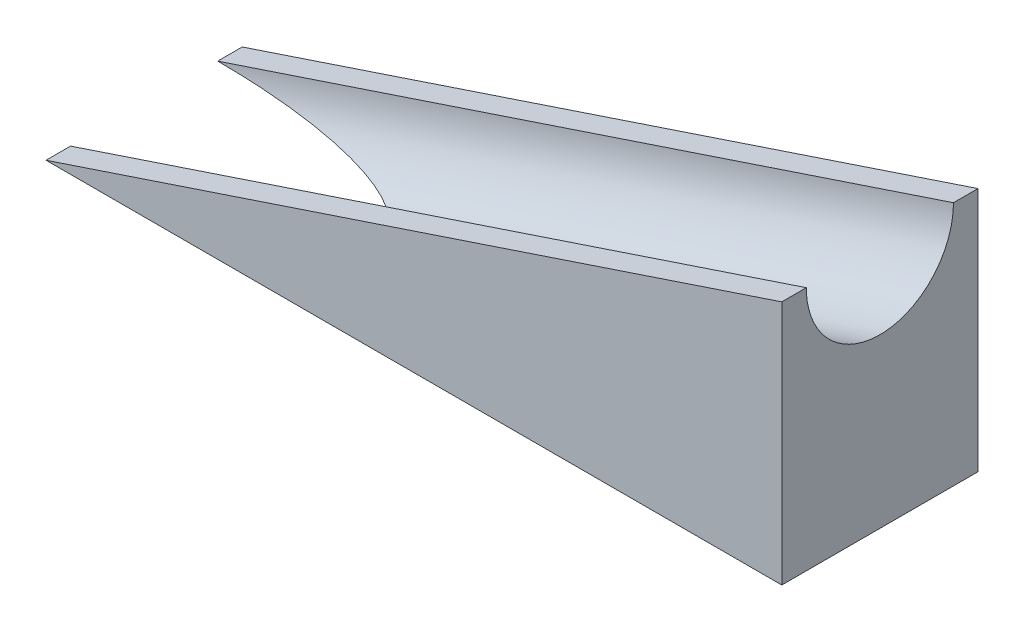
SolidWorks part; units mm, degrees
ref_plane "Front Plane" through (0, 0, 0) normal (0, 0, 1) x (1, 0, 0)
ref_plane "Top Plane" through (0, 0, 0) normal (0, 1, 0) x (1, 0, 0)
ref_plane "Right Plane" through (0, 0, 0) normal (1, 0, 0) x (0, 0, -1)
sketch "Sketch1" plane through (0, 0, 0) normal (0, 0, 1) x (1, 0, 0)
  line L0 (150, 50) -> (0, 0)
  line L1 (0, 0) -> (150, 0)
  line L4 (150, 0) -> (150, 50)
extrude "Boss-Extrude1" add sketch "Sketch1" along normal blind 40
sketch "Sketch3" plane through (0, 0, 0) normal (0, 0, -1) x (-1, 0, 0)
  line L2 (-150, 50) -> (-144.0752, 67.7744) construction
ref_plane "Plane1" through (150, 50, 0) normal (-0.9487, -0.3162, 0) x (0, 0, 1)
sketch "Sketch4" plane through (150, 50, 0) normal (-0.9487, -0.3162, 0) x (0, 0, 1)
  line L0 (40, 0) -> (0, 0) construction
  circle A0 centre (20, 0) radius 15
sketch3d "3DSketch1"
  line L0 (150, 50, 20) -> (0, 0, 20)
  line L1 (0, 0, 40) -> (0, 0, 0) construction
sweep "Cut-Sweep1" cut profiles "Sketch4" path "3DSketch1"
